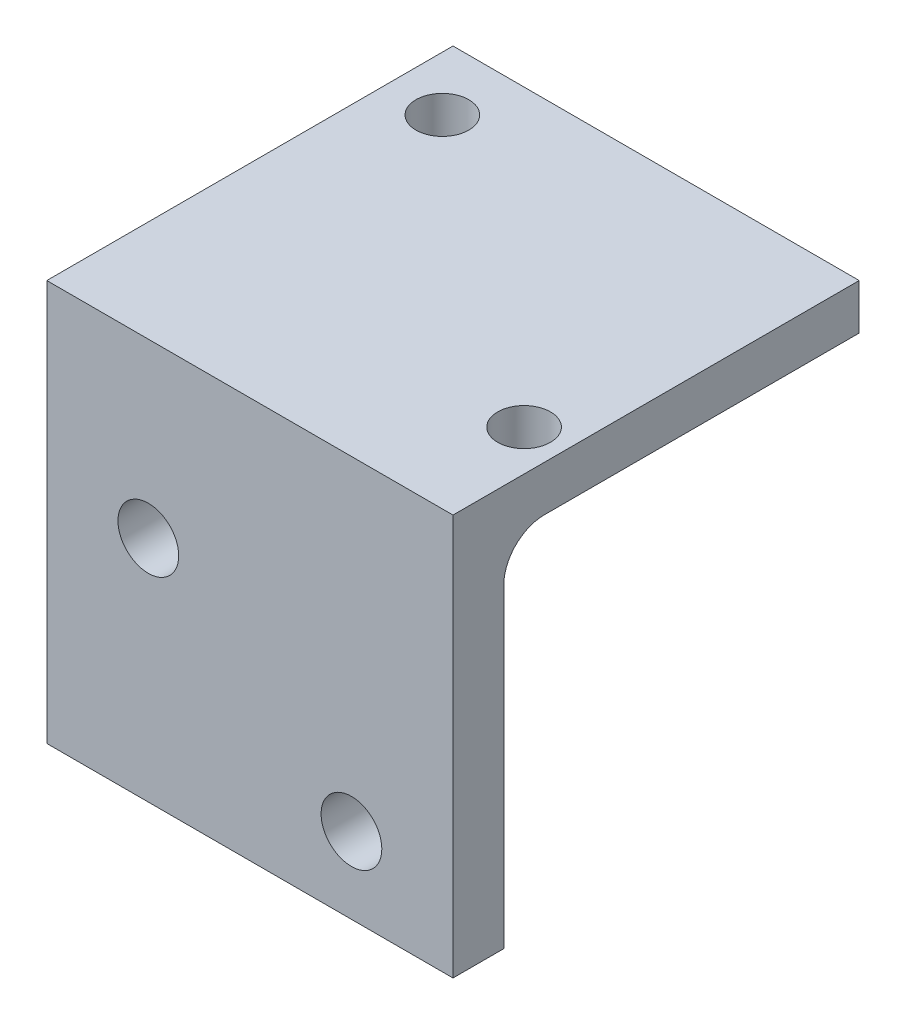
SolidWorks part; units mm, degrees
ref_plane "Front Plane" through (0, 0, 0) normal (0, 0, 1) x (1, 0, 0)
ref_plane "Top Plane" through (0, 0, 0) normal (0, 1, 0) x (1, 0, 0)
ref_plane "Right Plane" through (0, 0, 0) normal (1, 0, 0) x (0, 0, -1)
sketch "Sketch2" plane through (0, 0, 0) normal (0, 1, 0) x (1, 0, 0)
  line L1 (-25.5749, 13.5798) -> (-0.1749, 13.5798)
  line L2 (-25.5749, 13.5798) -> (-25.5749, -2.2952)
  line L3 (-25.5749, -2.2952) -> (-0.1749, -2.2952)
  line L4 (-0.1749, 13.5798) -> (-0.1749, -2.2952)
  line L5 (-0.1749, -2.2952) -> (-25.5749, -2.2952)
  line L6 (-0.1749, -2.2952) -> (-0.1749, -6.1052)
  line L7 (-0.1749, -6.1052) -> (-25.5749, -6.1052)
  line L8 (-25.5749, -2.2952) -> (-25.5749, -6.1052)
  line L9 (-0.1749, 13.5798) -> (-25.5749, 13.5798)
  line L10 (-0.1749, 13.5798) -> (-0.1749, 19.2948)
  line L11 (-0.1749, 19.2948) -> (-25.5749, 19.2948)
  line L12 (-25.5749, 13.5798) -> (-25.5749, 19.2948)
  circle A0 centre (-2.7149, 0.8798) radius 1.651
  circle A1 centre (-22.1757, 15.2308) radius 1.651
  dimension "D3" = 3.302
  dimension "D8" = 3.302
  dimension "D7" = 25.4
  dimension "D1" = 15.875
  dimension "D2" = 25.4
  dimension "D4" = 3.175
  dimension "D5" = 2.54
  dimension "D9" = 3.81
  dimension "D10" = 24.1801
extrude "Boss-Extrude1" add sketch "Sketch2" along normal blind 2.8448 contours L3 L8 L7 L6 | L4 L1 L2 L3 A1 A0 | L1 A1 L9 L10 L11 L12
sketch "Sketch3" plane through (0, 0, 0) normal (0, -1, 0) x (-1, 0, 0)
  line L0 (0.1749, 19.2948) -> (0.1749, -6.1052) construction
  line L1 (25.5749, -6.1052) -> (0.1749, -6.1052)
  line L2 (25.5749, -6.1052) -> (25.5749, -2.9302)
  line L3 (25.5749, -2.9302) -> (0.1749, -2.9302)
  line L4 (0.1749, -6.1052) -> (0.1749, -2.9302)
  dimension "D1" = 3.175
extrude "Boss-Extrude2" add sketch "Sketch3" along normal blind 22.225
fillet "Fillet1" radius 2.54 1 edges
hole_wizard "#6 Clearance Hole1" positions "3DSketch1" profile "Sketch4" hole size "#6" standard "ANSI Inch"
sketch3d "3DSketch1"
  line L0 (-25.5749, -22.225, 2.9302) -> (-0.1749, -22.225, 2.9302) construction
  line L1 (-0.1749, -22.225, 2.9302) -> (-0.1749, -2.54, 2.9302) construction
  line L2 (-25.5749, -22.225, 2.9302) -> (-25.5749, -2.54, 2.9302) construction
  point P0 (-6.5249, -17.4625, 2.9302)
  point P2 (-19.2249, -7.9375, 2.9302)
  dimension "D1" = 4.7625
  dimension "D2" = 14.2875
  dimension "D3" = 6.35
  dimension "D4" = 6.35
sketch "Sketch4" plane through (-6.5249, -17.4625, 2.9302) normal (1, 0, 0) x (0, 1, 0)
  line L0 (0, 0) -> (0, 13.8408)
  line L1 (0, 13.8408) -> (1.8986, 12.7)
  line L2 (1.8986, 12.7) -> (1.8986, 0)
  line L5 (1.8986, 0) -> (0, 0)
  line L10 (0, 13.8408) -> (-1.8986, 12.7) construction
  line L11 (0, -6.35) -> (0, 107.95) construction
  dimension "Hole Dia." = 3.7973
  dimension "Hole Depth" = 12.7
  dimension "Drill Angle" = 118
